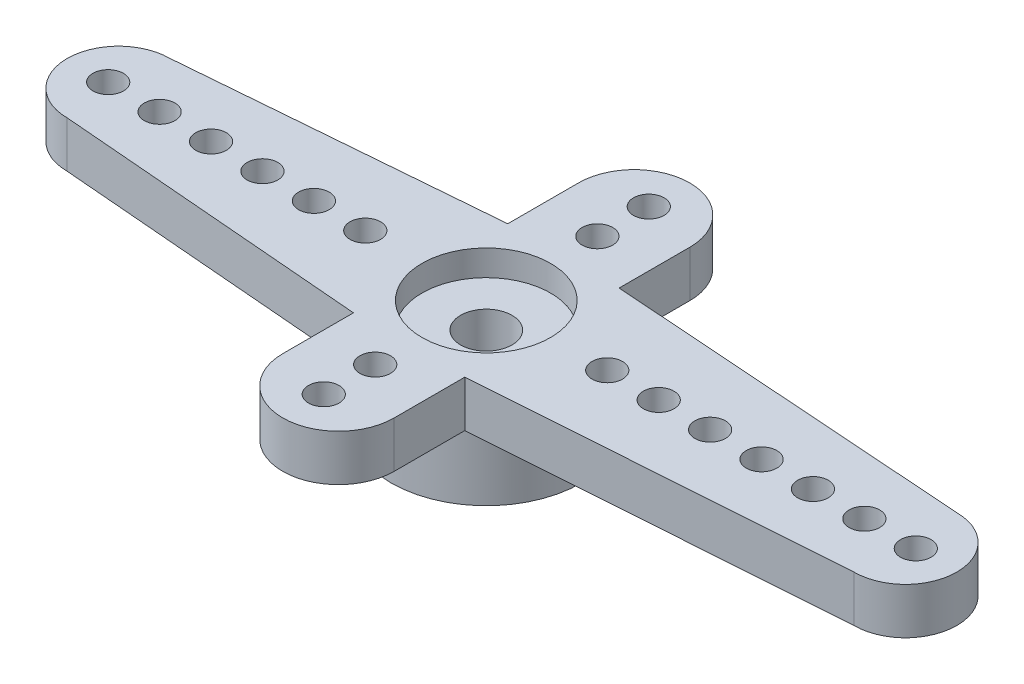
SolidWorks part; units mm, degrees
ref_plane "Alzado" through (0, 0, 0) normal (0, 0, 1) x (1, 0, 0)
ref_plane "Planta" through (0, 0, 0) normal (0, 1, 0) x (1, 0, 0)
ref_plane "Vista lateral" through (0, 0, 0) normal (1, 0, 0) x (0, 0, -1)
sketch "Croquis1" plane through (0, 0, 0) normal (0, 1, 0) x (1, 0, 0)
  circle A0 centre (0, 0) radius 3.7
  dimension "D1" = 7.4
extrude "Saliente-Extruir2" add sketch "Croquis1" along normal blind 4.3 contours A0
sketch "Croquis2" plane through (0, 0, 0) normal (0, -1, 0) x (1, 0, 0)
  circle A0 centre (0, 0) radius 2.5
  dimension "D1" = 5
extrude "Cortar-Extruir1" cut sketch "Croquis2" against normal blind 1.5
sketch "Croquis3" plane through (0, 4.3, 0) normal (0, 1, 0) x (1, 0, 0)
  circle A0 centre (0, 0) radius 2.5
  dimension "D1" = 5
extrude "Cortar-Extruir2" cut sketch "Croquis3" against normal blind 1
sketch "Croquis4" plane through (0, 3.3, 0) normal (0, 1, 0) x (1, 0, 0)
  circle A0 centre (0, 0) radius 1
  dimension "D1" = 2
extrude "Cortar-Extruir3" cut sketch "Croquis4" against normal blind 1.8
sketch "Croquis5" plane through (0, 4.3, 0) normal (0, 1, 0) x (1, 0, 0)
  line L0 (0, 0) -> (-2.1656, 0) construction
  line L1 (-2.1656, 3) -> (-3.1202, 0)
  line L2 (-3.1202, 0) -> (-2.1656, -3)
  line L3 (-2.1656, 0) -> (-2.5, 0) construction
  line L4 (-3.7, 0) -> (-16.3, 0) construction
  line L5 (-14.3, 0) -> (-14.3, 2) construction
  line L6 (-14.3, 0) -> (-14.3, -2) construction
  line L7 (-2.1656, 3) -> (-14.3, 2)
  line L8 (-2.1656, -3) -> (-14.3, -2)
  line L9 (0, 5.1944) -> (0, -4.3435) construction
  line L10 (3.1202, 0) -> (2.1656, -3)
  line L11 (2.1656, 3) -> (16.3, 2)
  line L12 (2.1656, -3) -> (16.3, -2)
  line L13 (2.1656, 3) -> (3.1202, 0)
  line L14 (3.7, 0) -> (18.3, 0) construction
  line L15 (16.3, 0) -> (16.3, 2) construction
  line L16 (16.3, 0) -> (16.3, -2) construction
  arc A0 (-14.3, 2) -> (-14.3, -2) centre (-14.3, 0) ccw
  arc A1 (16.3, 2) -> (16.3, -2) centre (16.3, 0) cw
  circle A3 centre (0, 0) radius 3.7 construction
  circle A4 centre (0, 0) radius 2.5 construction
  point P2 (-14.3, 0)
  point P30 (16.3, 0)
  dimension "D1" = 2.1656
  dimension "D2" = 12.6
  dimension "D3" = 2
  dimension "D4" = 2
  dimension "D5" = 2
  dimension "D6" = 14.6
  dimension "D7" = 2
extrude "Saliente-Extruir3" add sketch "Croquis5" against normal blind 1.8
sketch "Croquis6" plane through (0, 4.3, 0) normal (0, 1, 0) x (1, 0, 0)
  line L0 (0, 0) -> (-16.3, 0) construction
  line L1 (2, 0) -> (-14.3, 0) construction
  line L2 (4, 0) -> (-12.3, 0) construction
  line L3 (6, 0) -> (-10.3, 0) construction
  line L4 (8, 0) -> (-8.3, 0) construction
  line L5 (10, 0) -> (-6.3, 0) construction
  line L6 (0, 5.4913) -> (0, -4.5375) construction
  arc A0 (-14.3, 2) -> (-14.3, -2) centre (-14.3, 0) ccw construction
  circle A1 centre (-14.705, 0) radius 0.595
  circle A2 centre (-12.705, 0) radius 0.595
  circle A3 centre (-10.705, 0) radius 0.595
  circle A4 centre (-8.705, 0) radius 0.595
  circle A5 centre (-6.705, 0) radius 0.595
  circle A6 centre (-4.705, 0) radius 0.595
  circle A7 centre (14.705, 0) radius 0.595
  circle A8 centre (12.705, 0) radius 0.595
  circle A9 centre (10.705, 0) radius 0.595
  circle A10 centre (8.705, 0) radius 0.595
  circle A11 centre (6.705, 0) radius 0.595
  circle A12 centre (4.705, 0) radius 0.595
  circle A13 centre (16.705, 0) radius 0.595
  point P6 (-14.705, 0)
  dimension "D2" = 1.19
  dimension "D1" = 1.595
  dimension "D3" = 6
  dimension "D4" = 2
extrude "Cortar-Extruir4" cut sketch "Croquis6" against normal blind 1.8
sketch "Croquis7" plane through (0, 4.3, 0) normal (0, 1, 0) x (1, 0, 0)
  line L0 (-2.1656, 3) -> (2.1656, 3)
  line L1 (2.1656, 3) -> (2.1656, 5.75)
  line L2 (-2.1656, 3) -> (-2.1656, 5.75)
  line L3 (-16.3, 0) -> (18.3, 0) construction
  line L4 (0, 7.9156) -> (0, 6.3206) construction
  line L7 (0, 5.9156) -> (0, 4.3206) construction
  line L8 (2.1656, -3) -> (2.1656, -5.75)
  line L9 (-2.1656, -3) -> (-2.1656, -5.75)
  line L10 (-2.1656, -3) -> (2.1656, -3)
  line L11 (10, 7.9156) -> (10, 6.3206) construction
  line L12 (10, 5.9156) -> (10, 4.3206) construction
  arc A0 (2.1656, 5.75) -> (-2.1656, 5.75) centre (0, 5.75) ccw
  arc A1 (-14.3, 2) -> (-14.3, -2) centre (-14.3, 0) ccw construction
  arc A2 (16.3, -2) -> (16.3, 2) centre (16.3, 0) ccw construction
  circle A3 centre (0, 6.3206) radius 0.595
  circle A6 centre (0, 4.3206) radius 0.595
  circle A7 centre (0, -4.3206) radius 0.595
  circle A8 centre (0, -6.3206) radius 0.595
  arc A9 (2.1656, -5.75) -> (-2.1656, -5.75) centre (0, -5.75) cw
  circle A10 centre (10, 6.3206) radius 0.595 [skipped]
  circle A11 centre (10, 4.3206) radius 0.595 [skipped]
  dimension "D2" = 1.595
  dimension "D3" = 1.19
  dimension "D1" = 2.75
  dimension "D4" = 2
  dimension "D5" = 2
extrude "Saliente-Extruir4" add sketch "Croquis7" against normal blind 1.8
sketch "Sketch1" plane through (0, 4.3, 0) normal (0, 1, 0) x (1, 0, 0)
  line L16 (-14.3453, -2.9997) -> (-3.1656, -3.921)
  line L17 (-3.1656, -3.921) -> (-3.1656, -5.75)
  line L18 (3.1656, -5.75) -> (3.1656, -3.9318)
  line L19 (3.1656, -3.9318) -> (16.3389, -2.9997)
  line L20 (16.3389, 2.9997) -> (3.1656, 3.9318)
  line L21 (3.1656, 3.9318) -> (3.1656, 5.75)
  line L22 (-3.1656, 5.75) -> (-3.1656, 3.921)
  line L23 (-3.1656, 3.921) -> (-14.3453, 2.9997)
  line L24 (-14.3453, -2.9997) -> (-3.1656, -3.921)
  line L25 (-3.1656, -3.921) -> (-3.1656, -5.75)
  line L26 (3.1656, -5.75) -> (3.1656, -3.9318)
  line L27 (3.1656, -3.9318) -> (16.3389, -2.9997)
  line L28 (16.3389, 2.9997) -> (3.1656, 3.9318)
  line L29 (3.1656, 3.9318) -> (3.1656, 5.75)
  line L30 (-3.1656, 5.75) -> (-3.1656, 3.921)
  line L31 (-3.1656, 3.921) -> (-14.3453, 2.9997)
  arc A8 (-3.1656, -5.75) -> (3.1656, -5.75) centre (0, -5.75) ccw
  arc A9 (16.3389, -2.9997) -> (16.3389, 2.9997) centre (16.3, 0) ccw
  arc A10 (3.1656, 5.75) -> (-3.1656, 5.75) centre (0, 5.75) ccw
  arc A11 (-14.3453, 2.9997) -> (-14.3453, -2.9997) centre (-14.3, 0) ccw
  arc A12 (-3.1656, -5.75) -> (3.1656, -5.75) centre (0, -5.75) ccw
  arc A13 (16.3389, -2.9997) -> (16.3389, 2.9997) centre (16.3, 0) ccw
  arc A14 (3.1656, 5.75) -> (-3.1656, 5.75) centre (0, 5.75) ccw
  arc A15 (-14.3453, 2.9997) -> (-14.3453, -2.9997) centre (-14.3, 0) ccw
  dimension "D1" = 1
